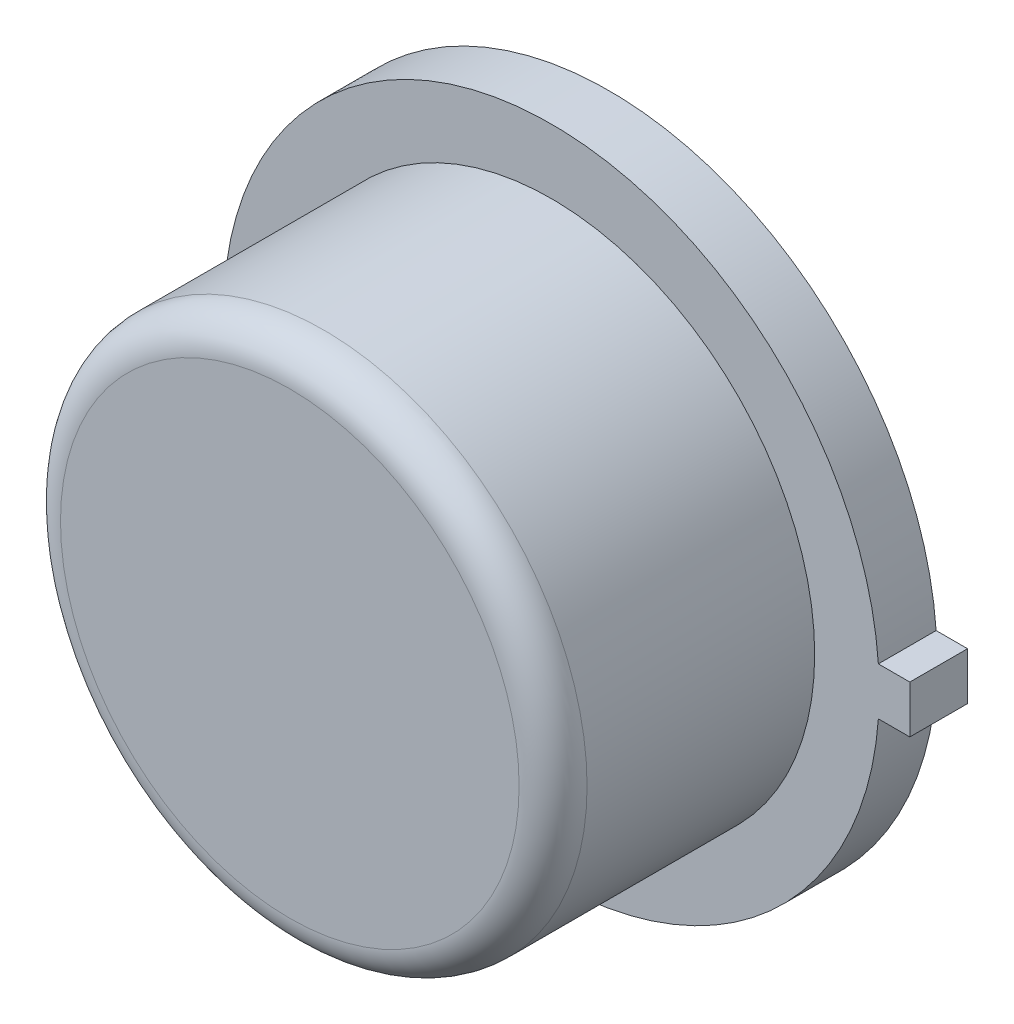
SolidWorks part; units mm, degrees
ref_plane "Front Plane" through (0, 0, 0) normal (0, 0, 1) x (1, 0, 0)
ref_plane "Top Plane" through (0, 0, 0) normal (0, 1, 0) x (1, 0, 0)
ref_plane "Right Plane" through (0, 0, 0) normal (1, 0, 0) x (0, 0, -1)
sketch "Sketch1" plane through (0, 0, 0) normal (0, 0, 1) x (1, 0, 0)
  line L1 (2.4511, 0.1778) -> (2.6797, 0.1778)
  line L3 (2.4511, -0.1778) -> (2.6797, -0.1778)
  line L4 (2.6797, 0.1778) -> (2.6797, -0.1778)
  line L5 (2.4511, 0.1778) -> (2.4444, 0.1778)
  line L6 (2.4511, -0.1778) -> (2.4446, -0.1778)
  arc A0 (2.4446, 0.1778) -> (2.4446, -0.1778) centre (0, 0) ccw
  dimension "D1" = 4.9022
  dimension "D2" = 0.3556
  dimension "D3" = 0.2286
extrude "Boss-Extrude1" add sketch "Sketch1" along normal blind 0.4318
sketch "Sketch2" plane through (0, 0, 0.4318) normal (0, 0, 1) x (1, 0, 0)
  circle A0 centre (0, 0) radius 1.9685
  dimension "D1" = 3.937
extrude "Boss-Extrude2" add sketch "Sketch2" along normal blind 1.9558
sketch "Sketch3" plane through (0, 0, 0) normal (0, 0, -1) x (-1, 0, 0)
  circle A0 centre (0, 0) radius 1.7576
extrude "Boss-Extrude3" add sketch "Sketch3" along normal blind 0.0025
fillet "Fillet1" radius 0.254 1 edges at (1.9685, 0, 2.3876)
sketch "Sketch4" plane through (0, 0, 2.3876) normal (0, 0, 1) x (1, 0, 0)
  line L0 (-1.0795, -1.332) -> (1.0795, -1.332) construction
  circle A0 centre (0, 0) radius 1.7145 construction
  dimension "D1" = 2.159
